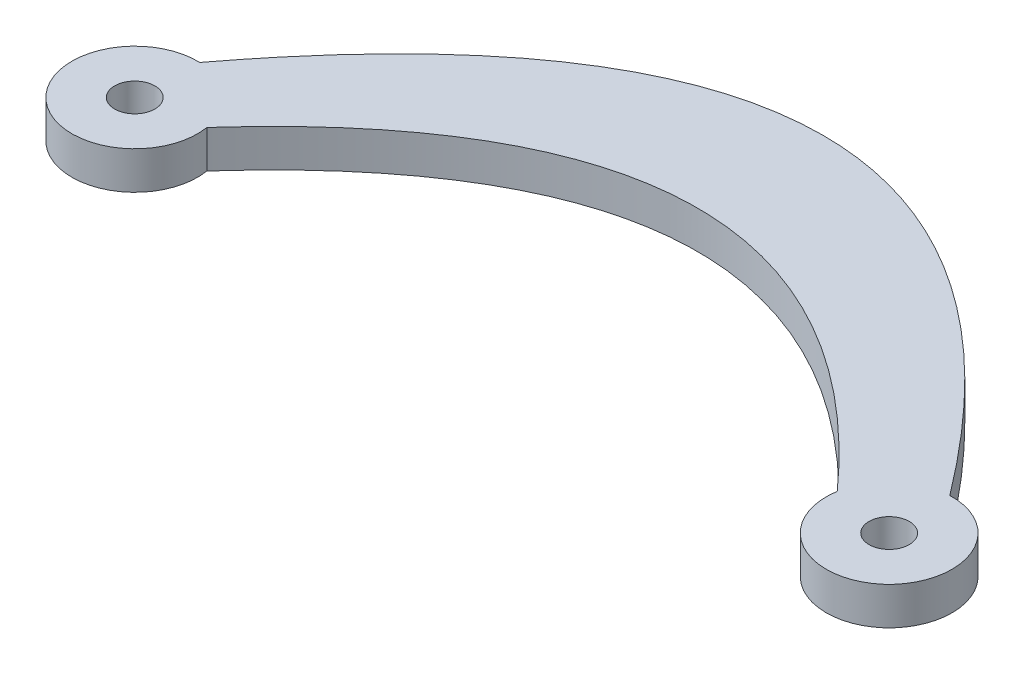
SolidWorks part; units mm, degrees
ref_plane "Front Plane" through (0, 0, 0) normal (0, 0, 1) x (1, 0, 0)
ref_plane "Top Plane" through (0, 0, 0) normal (0, 1, 0) x (1, 0, 0)
ref_plane "Right Plane" through (0, 0, 0) normal (1, 0, 0) x (0, 0, -1)
sketch "Sketch1" plane through (0, 0, 0) normal (0, 1, 0) x (1, 0, 0)
  line L0 (-30, 40) -> (-30, 0) construction
  line L1 (0, 0) -> (-60, 0) construction
  line L2 (0, 0.2335) -> (0, 40) construction
  line L3 (0, 40) -> (-60, 40) construction
  line L4 (-60, 10.2335) -> (-60, 40) construction
  arc A0 (-59.8267, 10.2305) -> (-55.0652, 6.0385) centre (-60, 5.2335) ccw
  arc A1 (-0.1733, 10.2305) -> (-4.9348, 6.0385) centre (0, 5.2335) cw
  circle A2 centre (-60, 5.2335) radius 1.6
  circle A3 centre (0, 5.2335) radius 1.6
  spline S1 degree 3 poles (-59.8267, 10.2305) (-49.8844, 23.4102) (-30, 36.5898) (-10.1156, 23.4102) (-0.1733, 10.2305) knots 0.002889 0.002889 0.002889 0.002889 0.5 0.997111 0.997111 0.997111 0.997111
  spline S2 degree 3 poles (-55.0652, 6.0385) (-46.7102, 15.3462) (-30, 24.6538) (-13.2898, 15.3462) (-4.9348, 6.0385) knots 0.082246 0.082246 0.082246 0.082246 0.5 0.917754 0.917754 0.917754 0.917754
  dimension "D6" = 10
  dimension "D3" = 3.2
  dimension "D1" = 60
  dimension "D2" = 40
extrude "Boss-Extrude1" add sketch "Sketch1" along normal blind 3
